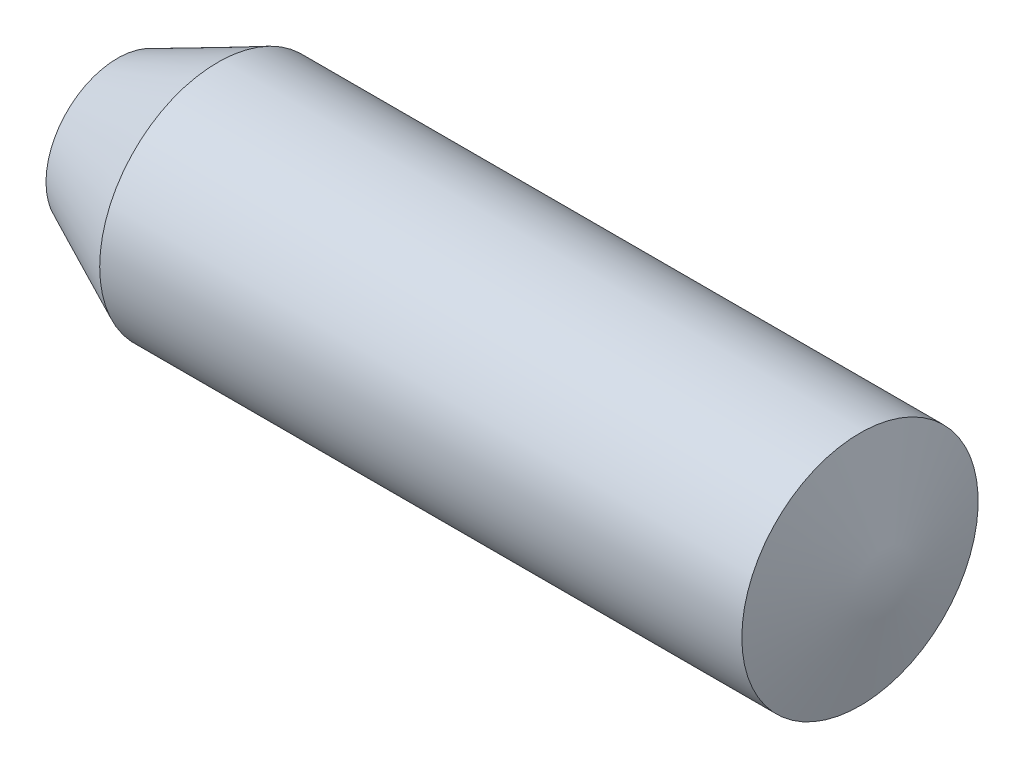
SolidWorks part; units mm, degrees
material "Cast Alloy Steel"
ref_plane "Front Plane" through (0, 0, 0) normal (0, 0, 1) x (1, 0, 0)
ref_plane "Top Plane" through (0, 0, 0) normal (0, 1, 0) x (1, 0, 0)
ref_plane "Right Plane" through (0, 0, 0) normal (1, 0, 0) x (0, 0, -1)
sketch "Sketch1" plane through (0, 0, 0) normal (0, 0, 1) x (1, 0, 0)
  line L0 (0, 0) -> (1828.8, 0) construction
  line L1 (0, 0) -> (0, 169.0969)
  line L2 (0, 169.0969) -> (237.2457, 279.4)
  line L3 (237.2457, 279.4) -> (1755.5085, 279.4)
  line L4 (1755.5085, 279.4) -> (1828.8, 0)
  line L5 (0, 0) -> (1828.8, 0)
  point P5 (914.4, 0)
  dimension "D1" = 1828.8
  dimension "D2" = 558.8
revolve "Revolve1" add sketch "Sketch1" angle 360 about L0
